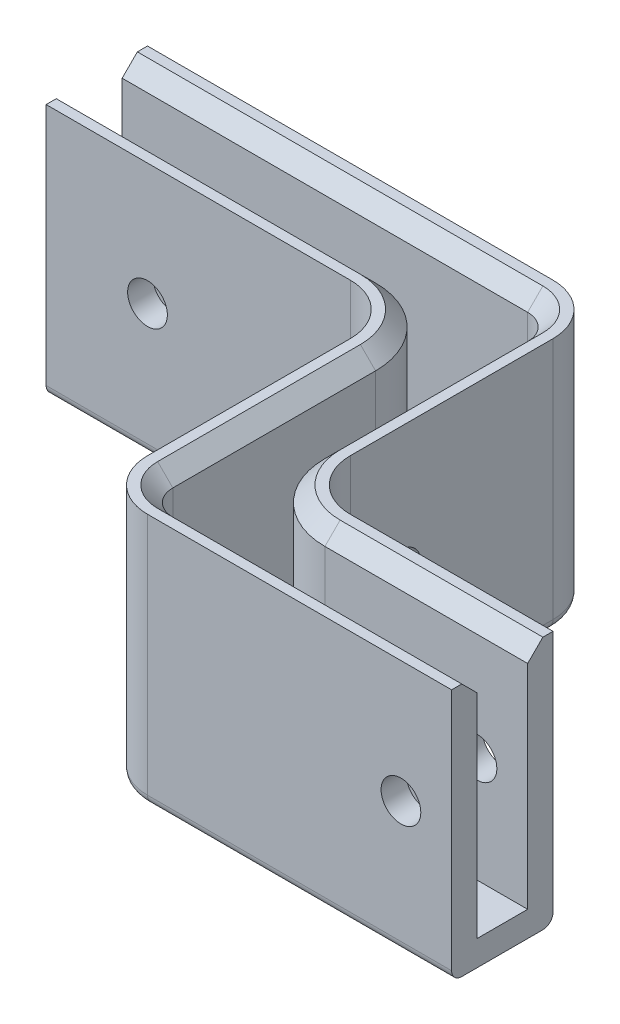
SolidWorks part; units mm, degrees
ref_plane "Front Plane" through (0, 0, 0) normal (0, 0, 1) x (1, 0, 0)
ref_plane "Top Plane" through (0, 0, 0) normal (0, 1, 0) x (1, 0, 0)
ref_plane "Right Plane" through (0, 0, 0) normal (1, 0, 0) x (0, 0, -1)
sketch "Sketch1" plane through (0, 0, 0) normal (0, 1, 0) x (1, 0, 0)
  line L0 (-57.15, 0) -> (0, 0)
  line L1 (0, 0) -> (0, -38.1)
  line L2 (0, -38.1) -> (31.75, -38.1)
  line L3 (31.75, -38.1) -> (31.75, -50.8)
  line L4 (31.75, -50.8) -> (-12.7, -50.8)
  line L5 (-12.7, -50.8) -> (-12.7, -12.7)
  line L6 (-12.7, -12.7) -> (-57.15, -12.7)
  line L7 (-57.15, -12.7) -> (-57.15, 0)
  line L8 (-12.7, -31.75) -> (0, -31.75) construction
  dimension "D1" = 12.7
  dimension "D2" = 25.4
  dimension "D3" = 57.15
  dimension "D4" = 44.45
extrude "Boss-Extrude1" add sketch "Sketch1" along normal blind 31.75
fillet "Fillet1" radius 6.35 4 edges at (-12.7, 15.875, 50.8) (-12.7, 15.875, 12.7) (0, 15.875, 38.1) (0, 15.875, 0)
shell "Shell1" thickness 3.175
fillet "Fillet2" radius 1.27 10 edges at (12.7, 0, 50.8) (-10.8401, 0, 48.9401) (-12.7, 0, 31.75) (-14.5599, 0, 14.5599) (19.05, 0, 38.1) (1.8599, 0, 36.2401) (0, 0, 19.05) (-1.8599, 0, 1.8599) (-38.1, 0, 12.7) (-31.75, 0, 0)
chamfer "Chamfer1" distance 1.905 angle 45 10 edges at (12.7, 31.75, 47.625) (-8.5951, 31.75, 46.6951) (-9.525, 31.75, 31.75) (-12.3148, 31.75, 12.3148) (-38.1, 31.75, 9.525) (19.05, 31.75, 41.275) (-0.3852, 31.75, 38.4852) (-3.175, 31.75, 19.05) (-4.1049, 31.75, 4.1049) (-31.75, 31.75, 3.175)
sketch "Sketch3" plane through (-12.7, 0, 0) normal (-1, 0, 0) x (0, 0, 1)
  line L0 (0, 15.875) -> (50.8, 15.875) construction
  line L1 (0, 31.75) -> (0, 1.27) construction
  line L2 (50.8, 31.75) -> (50.8, 1.27) construction
  line L3 (25.4, 31.75) -> (25.4, 0) construction
  line L4 (19.05, 31.75) -> (44.45, 31.75) construction
  line L5 (44.45, 0) -> (19.05, 0) construction
  point P12 (25.4, 15.875)
  point P15 (25.4, 15.875)
hole_wizard "#9 (0.196) Diameter Hole1" positions "Sketch3" profile "Sketch4" hole size "#9" standard "ANSI Inch" end condition through all
sketch "Sketch4" plane through (-12.7, 15.875, 25.4) normal (0, 1, 0) x (0, 0, 1)
  line L0 (0, 0) -> (0, 44.45)
  line L1 (0, 44.45) -> (2.4892, 44.45)
  line L2 (2.4892, 44.45) -> (2.4892, 0)
  line L5 (2.4892, 0) -> (0, 0)
  line L11 (0, -6.35) -> (0, 107.95) construction
  dimension "Thru Hole Dia." = 4.9784
  dimension "Thru Hole Depth" = 44.45
sketch "Sketch5" plane through (0, 0, 0) normal (0, 0, -1) x (-1, 0, 0)
  line L0 (57.15, 31.75) -> (57.15, 1.27) construction
  point P0 (44.45, 16.51)
  point P3 (57.15, 16.51)
  dimension "D1" = 12.7
hole_wizard "#9 (0.196) Diameter Hole2" positions "Sketch5" profile "Sketch6" hole size "#9" standard "ANSI Inch" end condition through all
sketch "Sketch6" plane through (-44.45, 16.51, 0) normal (1, 0, 0) x (0, 1, 0)
  line L0 (0, 0) -> (0, 50.8)
  line L1 (0, 50.8) -> (2.4892, 50.8)
  line L2 (2.4892, 50.8) -> (2.4892, 0)
  line L5 (2.4892, 0) -> (0, 0)
  line L11 (0, -6.35) -> (0, 107.95) construction
  dimension "Thru Hole Dia." = 4.9784
  dimension "Thru Hole Depth" = 50.8
sketch "Sketch7" plane through (0, 0, 50.8) normal (0, 0, 1) x (1, 0, 0)
  line L0 (31.75, 31.75) -> (31.75, 1.27) construction
  point P0 (25.4, 16.51)
  point P3 (31.75, 16.51)
  dimension "D1" = 6.35
hole_wizard "#9 (0.196) Diameter Hole3" positions "Sketch7" profile "Sketch8" hole size "#9" standard "ANSI Inch" end condition through all
sketch "Sketch8" plane through (25.4, 16.51, 50.8) normal (1, 0, 0) x (0, -1, 0)
  line L0 (0, 0) -> (0, 50.8)
  line L1 (0, 50.8) -> (2.4892, 50.8)
  line L2 (2.4892, 50.8) -> (2.4892, 0)
  line L5 (2.4892, 0) -> (0, 0)
  line L11 (0, -6.35) -> (0, 107.95) construction
  dimension "Thru Hole Dia." = 4.9784
  dimension "Thru Hole Depth" = 50.8
